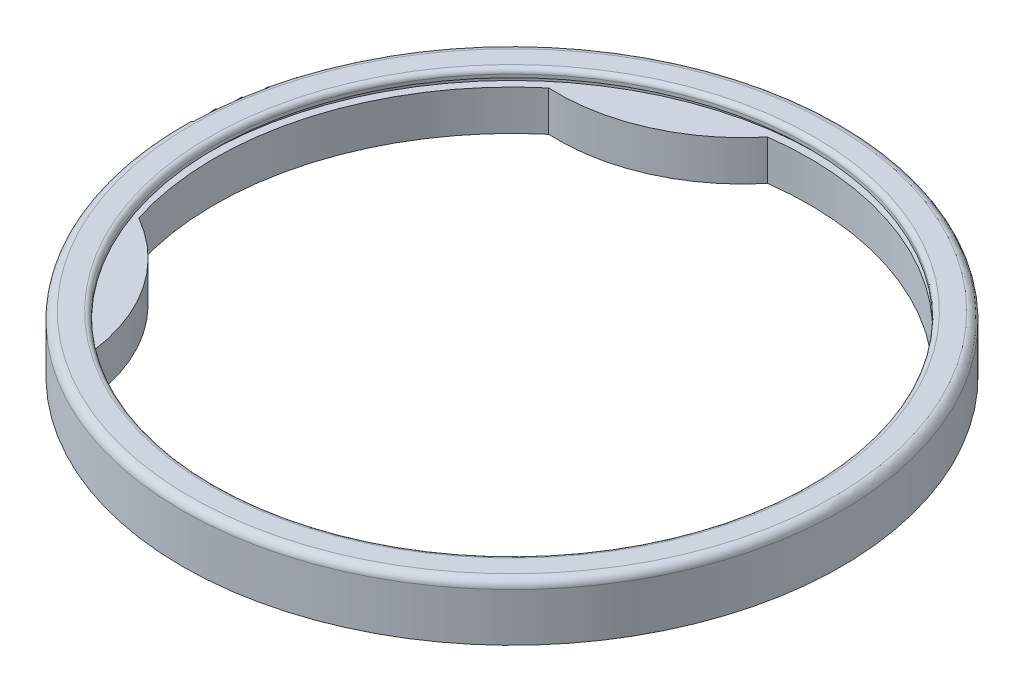
SolidWorks part; units mm, degrees
material "Oak"
ref_plane "Front Plane" through (0, 0, 0) normal (0, 0, 1) x (1, 0, 0)
ref_plane "Top Plane" through (0, 0, 0) normal (0, 1, 0) x (1, 0, 0)
ref_plane "Right Plane" through (0, 0, 0) normal (1, 0, 0) x (0, 0, -1)
sketch "Sketch2" plane through (0, 0, 0) normal (1, 0, 0) x (0, 0, -1)
  line L0 (-195, 0) -> (0, 0) construction
  line L1 (0, 0) -> (0, 23.4456) construction
  line L2 (-195, 0) -> (-195, -25) construction
  line L3 (-185, -25) -> (-205, -25)
  line L4 (-205, -25) -> (-205, 10)
  line L5 (-185, 10) -> (-205, 10)
  line L6 (-185, 10) -> (-185, 5)
  line L7 (-185, 5) -> (-190, 5)
  line L8 (-190, 5) -> (-190, 0)
  line L9 (-190, 0) -> (-185, 0)
  line L10 (-185, 0) -> (-185, -25)
  dimension "D1" = 25
  dimension "D2" = 195
  dimension "D3" = 20
  dimension "D4" = 10
  dimension "D5" = 5
  dimension "D6" = 5
  dimension "D7" = 5
  dimension "D8" = 20
revolve "Revolve1" add sketch "Sketch2" angle 360 about L1
fillet "Fillet1" radius 5 1 edges at (0, 10, -205)
fillet "Fillet2" radius 3 1 edges at (0, 10, -185)
sketch "Sketch15" plane through (0, 0, 0) normal (0, 1, 0) x (1, 0, 0)
  line L0 (-113.0637, 256.5945) -> (0, 0) construction
  line L1 (0, 0) -> (-312.3816, 90.8746) construction
  arc A0 (-24.375, 183.3872) -> (-118.8873, 141.7421) centre (-113.0637, 256.5945) cw
  circle A1 centre (0, 0) radius 185 construction
  arc A2 (-118.9441, -141.6944) -> (-176.3684, -55.8496) centre (-233.063, -155.9032) ccw
  circle A3 centre (0, 0) radius 185
  circle M4 centre (0, 0) radius 185
  dimension "D1" = 115
  dimension "D2" = 50
  dimension "D3" = 280.4
extrude "Boss-Extrude1" add sketch "Sketch15" against normal up to surface (25 mm away) contours A0 M4 | A2 M4 up to face at (0, -25, -185)
sketch "Sketch18" plane through (0, 0, 0) normal (0, 1, 0) x (1, 0, 0)
  line L1 (0, 0) -> (-312.3816, 90.8746) construction
  line L2 (0, 0) -> (-312.3816, 90.8746)
sketch "Sketch21" plane through (0, 0, 0) normal (0, 1, 0) x (1, 0, 0)
  line L0 (0, 0) -> (-312.3816, 90.8746) construction
  line L1 (0, 0) -> (-312.3816, 90.8746)
sketch "Sketch24" plane through (0, 0, 0) normal (0, 1, 0) x (1, 0, 0)
  line L0 (-113.0637, 256.5945) -> (0, 0) construction
  line L1 (0, 0) -> (-312.3816, 90.8746) construction
  line L2 (0, 0) -> (-312.3816, 90.8746)
  circle A0 centre (-74.5962, 169.2938) radius 10
  circle A1 centre (0, 0) radius 185 construction
  circle A2 centre (-153.7684, -102.8605) radius 10
extrude "Cut-Extrude3" cut sketch "Sketch24" against normal through all from offset 5 contours A0 | A2
